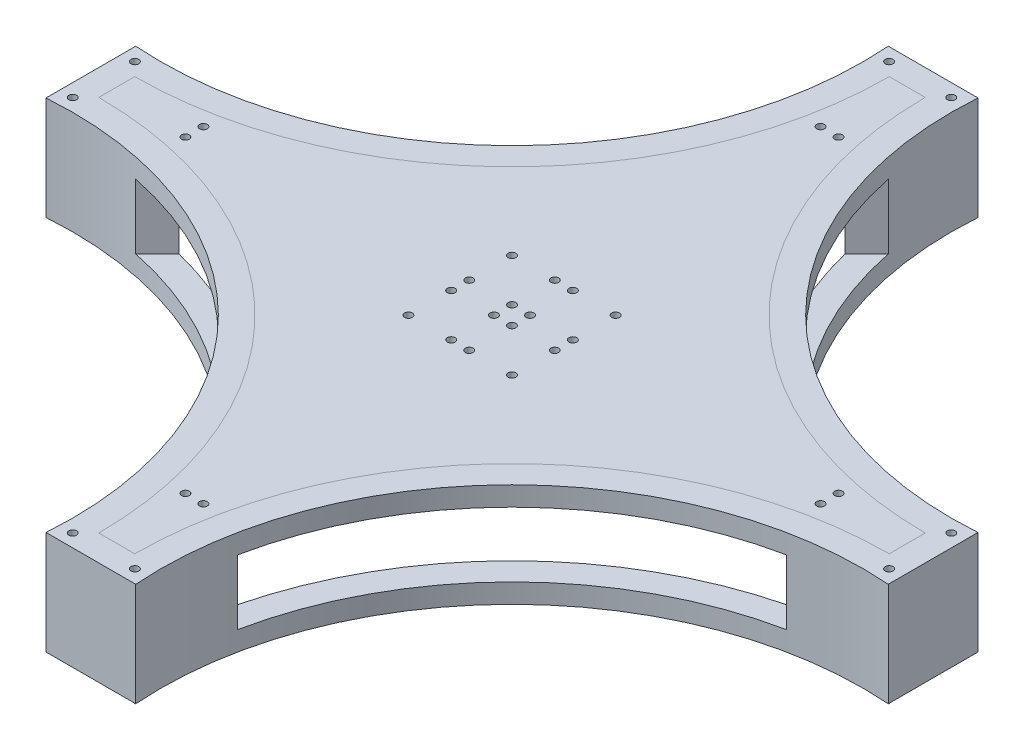
SolidWorks part; units mm, degrees
ref_plane "Front Plane" through (0, 0, 0) normal (0, 0, 1) x (1, 0, 0)
ref_plane "Top Plane" through (0, 0, 0) normal (0, 1, 0) x (1, 0, 0)
ref_plane "Right Plane" through (0, 0, 0) normal (1, 0, 0) x (0, 0, -1)
sketch "Sketch1" plane through (0, 0, 0) normal (0, 1, 0) x (1, 0, 0)
  line L0 (0, 0) -> (0, 152.66) construction
  line L1 (-6.96, 152.66) -> (6.96, 152.66)
  line L2 (0, 0) -> (152.66, 0) construction
  line L3 (152.66, -6.96) -> (152.66, 6.96)
  line L4 (-152.66, -6.96) -> (-152.66, 6.96)
  line L5 (-6.96, -152.66) -> (6.96, -152.66)
  arc A0 (6.96, 152.66) -> (152.66, 6.96) centre (152.66, 152.66) ccw
  arc A1 (-6.96, 152.66) -> (-152.66, 6.96) centre (-152.66, 152.66) cw
  arc A2 (6.96, -152.66) -> (152.66, -6.96) centre (152.66, -152.66) cw
  arc A3 (-6.96, -152.66) -> (-152.66, -6.96) centre (-152.66, -152.66) ccw
  point P16 (-152.66, 0)
  dimension "D1" = 152.66
  dimension "D2" = 6.96
  dimension "D3" = 152.66
  dimension "D4" = 6.96
extrude "Boss-Extrude1" add sketch "Sketch1" along normal blind 4
sketch "Sketch3" plane through (0, 0, 0) normal (0, -1, 0) x (1, 0, 0)
  line L0 (6.96, -152.66) -> (-6.96, -152.66) construction
  line L1 (-152.66, -6.96) -> (-152.66, 6.96) construction
  line L2 (-6.96, 152.66) -> (6.96, 152.66) construction
  line L3 (152.66, 6.96) -> (152.66, -6.96) construction
  line L4 (0.0044, -0.0044) -> (0.0044, -152.6687) construction
  line L5 (0.0044, -152.6687) -> (-6.96, -152.6687) construction
  line L6 (-152.66, -6.9687) -> (-152.66, -0.0044) construction
  line L7 (-152.66, -0.0044) -> (0.0044, -0.0044) construction
  line L8 (6.96, -152.66) -> (-6.96, -152.66)
  line L9 (-152.66, -6.96) -> (-152.66, 6.96)
  line L10 (-6.96, 152.66) -> (6.96, 152.66)
  line L11 (152.66, 6.96) -> (152.66, -6.96)
  line L12 (0.0044, -0.0044) -> (0.0044, -152.6687)
  line L13 (0.0044, -152.6687) -> (-6.96, -152.6687)
  line L14 (-152.66, -6.9687) -> (-152.66, -0.0044)
  line L15 (-152.66, -0.0044) -> (0.0044, -0.0044)
  arc A0 (152.66, -6.96) -> (6.96, -152.66) centre (152.66, -152.66) ccw construction
  arc A1 (-6.96, -152.66) -> (-152.66, -6.96) centre (-152.66, -152.66) ccw construction
  arc A2 (-152.66, 6.96) -> (-6.96, 152.66) centre (-152.66, 152.66) ccw construction
  arc A3 (6.96, 152.66) -> (152.66, 6.96) centre (152.66, 152.66) ccw construction
  arc A4 (-6.96, -152.6687) -> (-152.66, -6.9687) centre (-152.66, -152.6687) ccw construction
  circle A5 centre (-3.4778, -20.0065) radius 1.5 construction
  circle A6 centre (-3.4778, -3.4865) radius 1.5 construction
  circle A7 centre (-19.9956, -3.4865) radius 1.5 construction
  circle A8 centre (-19.9956, -20.0065) radius 1.5 construction
  circle A9 centre (-122.66, -3.4865) radius 1.5 construction
  arc A10 (152.66, -6.96) -> (6.96, -152.66) centre (152.66, -152.66) ccw
  arc A11 (-6.96, -152.66) -> (-152.66, -6.96) centre (-152.66, -152.66) ccw
  arc A12 (-152.66, 6.96) -> (-6.96, 152.66) centre (-152.66, 152.66) ccw
  arc A13 (6.96, 152.66) -> (152.66, 6.96) centre (152.66, 152.66) ccw
  arc A14 (-6.96, -152.6687) -> (-152.66, -6.9687) centre (-152.66, -152.6687) ccw
  circle A15 centre (-3.4778, -20.0065) radius 1.5
  circle A16 centre (-3.4778, -3.4865) radius 1.5
  circle A17 centre (-19.9956, -3.4865) radius 1.5
  circle A18 centre (-19.9956, -20.0065) radius 1.5
  circle A19 centre (-122.66, -3.4865) radius 1.5
extrude "Cut-Extrude1" cut sketch "Sketch3" against normal blind 100 contours A17 | A16 | A15 | A18 | A19
sketch "Sketch4" plane through (0, 0, 0) normal (0, -1, 0) x (1, 0, 0)
  circle A0 centre (-3.4778, -122.6687) radius 1.5 construction
  circle A1 centre (-3.4778, -122.6687) radius 1.5
extrude "Cut-Extrude2" cut sketch "Sketch4" against normal blind 100
sketch "Sketch5" plane through (0, 0, 0) normal (1, 0, 0) x (0, 0, -1)
  line L0 (0, 0) -> (0, 5.1214)
pattern_circular "CirPattern1" count 4 over 360 about axis through (0, 0, 0) along (0, 1, 0) of "Cut-Extrude2", "Cut-Extrude1"
sketch "Sketch6" plane through (0, 4, 0) normal (0, 1, 0) x (1, 0, 0)
  line L0 (17.329, 162.66) -> (-17.329, 162.66)
  line L1 (162.66, -17.329) -> (162.66, 17.329)
  line L2 (-17.329, -162.66) -> (17.329, -162.66)
  line L3 (-162.66, 17.329) -> (-162.66, -17.329)
  line L4 (6.96, 152.66) -> (-6.96, 152.66)
  line L5 (-152.66, 6.96) -> (-152.66, -6.96)
  line L6 (-6.96, -152.66) -> (6.96, -152.66)
  line L7 (152.66, -6.96) -> (152.66, 6.96)
  line L8 (6.96, 152.66) -> (-6.96, 152.66)
  line L9 (-152.66, 6.96) -> (-152.66, -6.96)
  line L10 (-6.96, -152.66) -> (6.96, -152.66)
  line L11 (152.66, -6.96) -> (152.66, 6.96)
  arc A0 (-162.66, 17.329) -> (-17.329, 162.66) centre (-152.66, 152.66) ccw
  arc A1 (17.329, 162.66) -> (162.66, 17.329) centre (152.66, 152.66) ccw
  arc A2 (162.66, -17.329) -> (17.329, -162.66) centre (152.66, -152.66) ccw
  arc A3 (-17.329, -162.66) -> (-162.66, -17.329) centre (-152.66, -152.66) ccw
  arc A4 (6.96, 152.66) -> (152.66, 6.96) centre (152.66, 152.66) ccw
  arc A5 (-152.66, 6.96) -> (-6.96, 152.66) centre (-152.66, 152.66) ccw
  arc A6 (-6.96, -152.66) -> (-152.66, -6.96) centre (-152.66, -152.66) ccw
  arc A7 (152.66, -6.96) -> (6.96, -152.66) centre (152.66, -152.66) ccw
  arc A8 (6.96, 152.66) -> (152.66, 6.96) centre (152.66, 152.66) ccw
  arc A9 (-152.66, 6.96) -> (-6.96, 152.66) centre (-152.66, 152.66) ccw
  arc A10 (-6.96, -152.66) -> (-152.66, -6.96) centre (-152.66, -152.66) ccw
  arc A11 (152.66, -6.96) -> (6.96, -152.66) centre (152.66, -152.66) ccw
  dimension "D1" = 0
  dimension "D2" = 10
extrude "Boss-Extrude2" add sketch "Sketch6" against normal blind 40 separate body
ref_plane "Plane1" through (-17.329, -36, -162.66) normal (0.0737, 0, 0.9973) x (0.9973, 0, -0.0737)
sketch "Sketch8" plane through (0, -36, 0) normal (0, -1, 0) x (1, 0, 0)
  circle A0 centre (-157.66, 12) radius 1.5 construction
  circle A1 centre (-157.66, -12) radius 1.5 construction
  circle A2 centre (-157.66, 12) radius 1.5
  circle A3 centre (-157.66, -12) radius 1.5
  circle A4 centre (-12, 157.66) radius 1.5 construction
  circle A5 centre (12, 157.66) radius 1.5 construction
  circle A6 centre (157.66, -12) radius 1.5 construction
  circle A7 centre (157.66, 12) radius 1.5 construction
  circle A8 centre (-12, -157.66) radius 1.5 construction
  circle A9 centre (12, -157.66) radius 1.5 construction
  circle A10 centre (-12, 157.66) radius 1.5
  circle A11 centre (12, 157.66) radius 1.5
  circle A12 centre (157.66, -12) radius 1.5
  circle A13 centre (157.66, 12) radius 1.5
  circle A14 centre (-12, -157.66) radius 1.5
  circle A15 centre (12, -157.66) radius 1.5
extrude "Cut-Extrude3" cut sketch "Sketch8" against normal up to surface (40 mm away) up to face at (0, 4, 0)
ref_plane "Plane2" through (89.9945, 0, -89.9945) normal (-0.7071, 0, 0.7071) x (0.7071, 0, 0.7071)
sketch "Sketch9" plane through (89.9945, 0, -89.9945) normal (-0.7071, 0, 0.7071) x (0.7071, 0, 0.7071)
  line L0 (102.7646, -36) -> (102.7646, 4) construction
  line L1 (-102.7646, -36) -> (-102.7646, 4) construction
  line L2 (102.7646, -16) -> (-102.7646, -16) construction
  line L4 (75, -28.5) -> (-75, -28.5)
  line L5 (75, -28.5) -> (75, -3.5)
  line L6 (75, -3.5) -> (-75, -3.5)
  line L7 (-75, -28.5) -> (-75, -3.5)
  line L8 (75, -28.5) -> (-75, -3.5) construction
  line L9 (75, -3.5) -> (-75, -28.5) construction
  point P0 (102.7646, -16)
  point P1 (-102.7646, -16)
  point P8 (0, -16)
  dimension "D1" = 25
  dimension "D2" = 150
extrude "Cut-Extrude7" cut sketch "Sketch9" along normal blind 59
pattern_circular "CirPattern2" count 4 over 360 about axis through (0, 0, 0) along (0, 1, 0) of "Cut-Extrude7"
